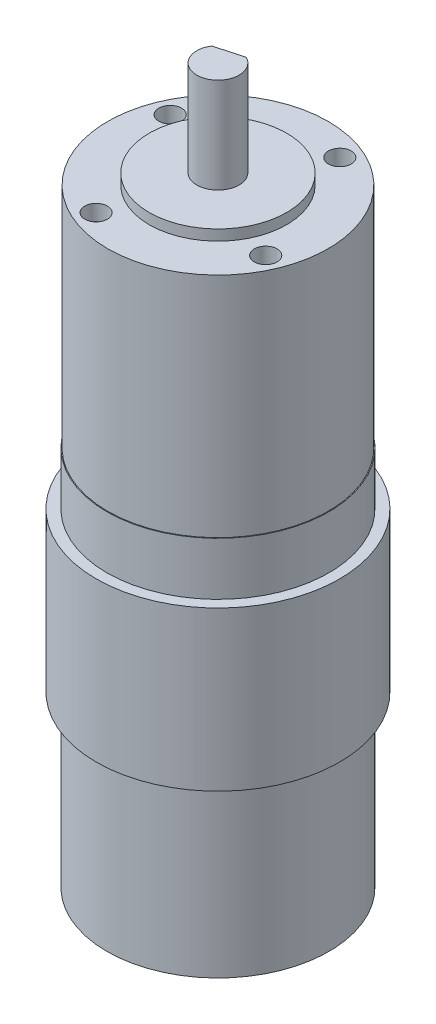
SolidWorks part; units mm, degrees
ref_plane "Front Plane" through (0, 0, 0) normal (0, 0, 1) x (1, 0, 0)
ref_plane "Top Plane" through (0, 0, 0) normal (0, 1, 0) x (1, 0, 0)
ref_plane "Right Plane" through (0, 0, 0) normal (1, 0, 0) x (0, 0, -1)
sketch "Sketch1" plane through (0, 0, 0) normal (0, 1, 0) x (1, 0, 0)
  circle A0 centre (0, 0) radius 21
  dimension "D1" = 42
extrude "Boss-Extrude1" add sketch "Sketch1" along normal blind 72
ref_plane "Plane1" through (0, 62, 0) normal (0, 1, 0) x (1, 0, 0)
sketch "Sketch3" plane through (0, 62, 0) normal (0, 1, 0) x (1, 0, 0)
  circle A0 centre (0, 0) radius 21
  circle A1 centre (0, 0) radius 23
  dimension "D1" = 42
  dimension "D2" = 46
extrude "Boss-Extrude2" add sketch "Sketch3" against normal blind 30
sketch "Sketch4" plane through (0, 72, 0) normal (0, 1, 0) x (1, 0, 0)
  circle A0 centre (0, 0) radius 20.85
  dimension "D1" = 41.7
extrude "Boss-Extrude3" add sketch "Sketch4" along normal blind 43
sketch "Sketch5" plane through (0, 115, 0) normal (0, 1, 0) x (1, 0, 0)
  circle A0 centre (0, 0) radius 13
  dimension "D1" = 26
extrude "Boss-Extrude4" add sketch "Sketch5" along normal blind 2
sketch "Sketch6" plane through (0, 117, 0) normal (0, 1, 0) x (1, 0, 0)
  circle A0 centre (0, 0) radius 4
  dimension "D1" = 8
extrude "Boss-Extrude5" add sketch "Sketch6" along normal blind 18
sketch "Sketch8" plane through (0, 0, 0) normal (0, -1, 0) x (1, 0, 0)
  circle A0 centre (0, 0) radius 7.5
  dimension "D1" = 15
extrude "Boss-Extrude6" add sketch "Sketch8" along normal blind 5
sketch "Sketch9" plane through (0, 117, 0) normal (0, 1, 0) x (1, 0, 0)
  circle A0 centre (0, 0) radius 17.5 construction
  dimension "D1" = 35
hole_wizard "CSK for M4 Flat Head Machine Screw1" positions "3DSketch1" profile "Sketch14" countersink size "M4" standard "ANSI Metric"
sketch3d "3DSketch1"
  circle A0 centre (0, 117, 0) radius 17.5 construction
  point P0 (-16.0363, 117, -7.0062)
  point P4 (0, 134.5, 0)
sketch "Sketch14" plane through (-16.0363, 117, -7.0062) normal (1, 0, 0) x (0, 0, 1)
  line L0 (0, 0) -> (0, 6.2919)
  line L1 (0, 6.2919) -> (2.15, 5)
  line L2 (2.15, 5) -> (2.15, 0.6)
  line L3 (2.15, 0.6) -> (2.75, 0)
  line L5 (2.75, 0) -> (0, 0)
  line L6 (-2.15, 0.6) -> (-2.75, 0) construction
  line L10 (0, 6.2919) -> (-2.15, 5) construction
  line L11 (0, -6.35) -> (0, 107.95) construction
  dimension "Hole Dia." = 4.3
  dimension "Hole Depth" = 5
  dimension "Near C'Sink Dia." = 5.5
  dimension "Near C'Sink Angle" = 90
  dimension "Drill Angle" = 118
pattern_circular "CirPattern1" count 4 over 360 about axis through (0, 0, 0) along (0, 1, 0) of "CSK for M4 Flat Head Machine Screw1"
sketch "Sketch16" plane through (0, 115, 0) normal (0, 1, 0) x (1, 0, 0)
  circle A0 centre (7.0062, 16.0363) radius 2.15 construction
  dimension "D1" = 4.3
sketch "Sketch17" plane through (0, 135, 0) normal (0, 1, 0) x (1, 0, 0)
  line L0 (-3.3456, 2.1924) -> (1.757, 3.5935)
  circle A0 centre (0, 0) radius 4 construction
  arc A1 (1.757, 3.5935) -> (-3.3456, 2.1924) centre (0, 0) ccw
  dimension "D1" = 3
extrude "Cut-Extrude1" cut sketch "Sketch17" against normal blind 10
